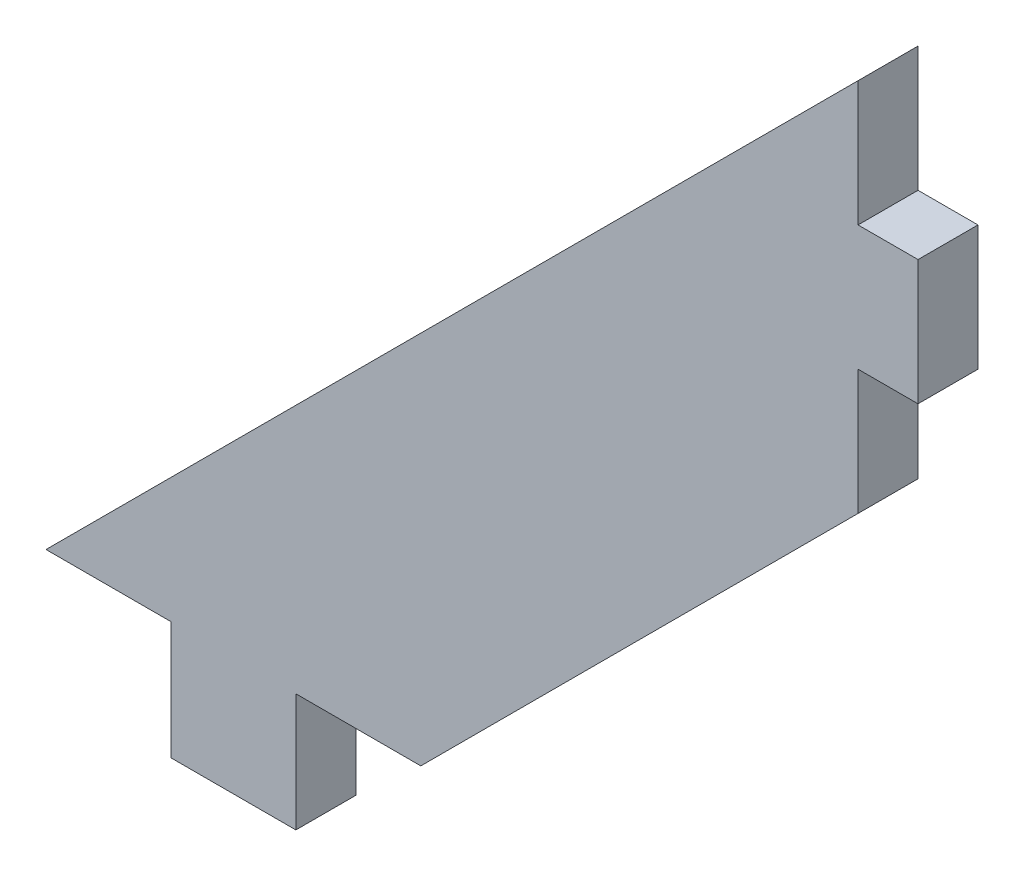
SolidWorks part; units mm, degrees
material "Acrylic (Medium-high impact)"
ref_plane "Front Plane" through (0, 0, 0) normal (0, 0, 1) x (1, 0, 0)
ref_plane "Top Plane" through (0, 0, 0) normal (0, 1, 0) x (1, 0, 0)
ref_plane "Right Plane" through (0, 0, 0) normal (1, 0, 0) x (0, 0, -1)
sketch "Sketch1" plane through (0, 0, 0) normal (0, 0, 1) x (1, 0, 0)
  line L0 (0, 0) -> (6.35, 0)
  line L1 (6.35, 0) -> (6.35, -5.9944)
  line L2 (6.35, -5.9944) -> (12.7, -5.9944)
  line L3 (12.7, -5.9944) -> (12.7, 0)
  line L4 (12.7, 0) -> (19.05, 0)
  line L5 (19.05, 0) -> (41.275, 22.225)
  line L6 (41.275, 22.225) -> (41.275, 28.575)
  line L7 (41.275, 28.575) -> (44.323, 28.575)
  line L8 (44.323, 28.575) -> (44.323, 34.925)
  line L9 (44.323, 34.925) -> (41.275, 34.925)
  line L10 (41.275, 34.925) -> (41.275, 41.275)
  line L11 (41.275, 41.275) -> (0, 0)
  dimension "D1" = 45
  dimension "D2" = 3.048
  dimension "D3" = 5.9944
  dimension "D4" = 6.35
  dimension "D5" = 6.35
  dimension "D6" = 34.925
  dimension "D7" = 41.275
  dimension "D8" = 28.575
extrude "Boss-Extrude1" add sketch "Sketch1" along normal blind 3.048
